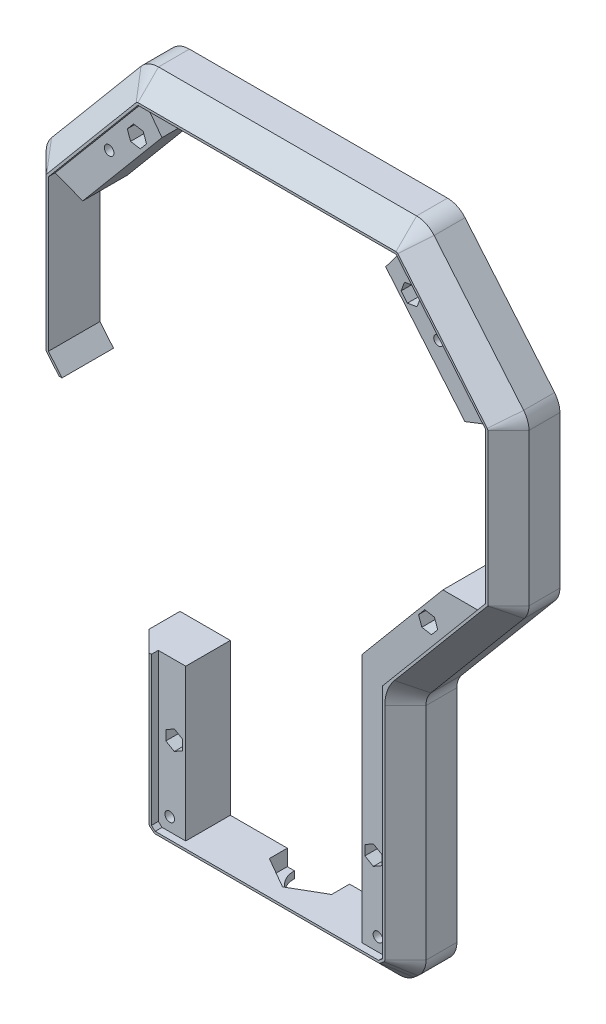
SolidWorks part; units mm, degrees
ref_plane "Plano frontal" through (0, 0, 0) normal (0, 0, 1) x (1, 0, 0)
ref_plane "Plano superior" through (0, 0, 0) normal (0, 1, 0) x (1, 0, 0)
ref_plane "Plano direito" through (0, 0, 0) normal (1, 0, 0) x (0, 0, -1)
sketch "Esboço1" plane through (0, 0, 0) normal (0, 0, 1) x (1, 0, 0)
  line L0 (-56.3875, 290.1973) -> (56.3875, 290.1973)
  line L1 (-60.5, 10.6056) -> (-60.5, 106.9588)
  line L2 (-62.6215, 112.7876) -> (-103.3785, 161.3599)
  line L3 (-105.5, 167.1887) -> (-105.5, 233.5849)
  line L4 (-48.8691, 270.1973) -> (48.8691, 270.1973)
  line L5 (0, 290.1973) -> (0, 0) construction
  line L6 (-64.0479, 286.6252) -> (-103.1604, 240.0128)
  line L7 (-83.5, 171.8956) -> (-83.5, 228.9258)
  line L8 (-83.5, 228.9258) -> (-48.8691, 270.1973)
  line L9 (-38.5, 19.1973) -> (38.5, 19.1973)
  line L10 (-38.5, 19.1973) -> (-38.5, 118.2666)
  line L11 (-38.5, 118.2666) -> (-83.5, 171.8956)
  line L12 (-56.9279, 2.9452) -> (-55.2496, 1.5369)
  line L13 (-48.8217, -0.8027) -> (48.8217, -0.8027)
  line L14 (56.9279, 2.9452) -> (55.2496, 1.5369)
  line L15 (38.5, 118.2666) -> (83.5, 171.8956)
  line L16 (38.5, 19.1973) -> (38.5, 118.2666)
  line L17 (83.5, 228.9258) -> (48.8691, 270.1973)
  line L18 (83.5, 171.8956) -> (83.5, 228.9258)
  line L19 (64.0479, 286.6252) -> (103.1604, 240.0128)
  line L20 (105.5, 167.1887) -> (105.5, 233.5849)
  line L21 (62.6215, 112.7876) -> (103.3785, 161.3599)
  line L22 (60.5, 10.6056) -> (60.5, 106.9588)
  arc A0 (-105.5, 233.5849) -> (-103.1604, 240.0128) centre (-95.5, 233.5849) cw
  arc A1 (-103.3785, 161.3599) -> (-105.5, 167.1887) centre (-96.4321, 167.1887) cw
  arc A2 (-60.5, 106.9588) -> (-62.6215, 112.7876) centre (-69.5679, 106.9588) ccw
  arc A3 (56.3875, 290.1973) -> (64.0479, 286.6252) centre (56.3875, 280.1973) cw
  arc A4 (-56.3875, 290.1973) -> (-64.0479, 286.6252) centre (-56.3875, 280.1973) ccw
  arc A5 (60.5, 106.9588) -> (62.6215, 112.7876) centre (69.5679, 106.9588) cw
  arc A6 (103.3785, 161.3599) -> (105.5, 167.1887) centre (96.4321, 167.1887) ccw
  arc A7 (105.5, 233.5849) -> (103.1604, 240.0128) centre (95.5, 233.5849) ccw
  arc A8 (56.9279, 2.9452) -> (60.5, 10.6056) centre (50.5, 10.6056) ccw
  arc A9 (55.2496, 1.5369) -> (48.8217, -0.8027) centre (48.8217, 9.1973) cw
  arc A10 (-48.8217, -0.8027) -> (-55.2496, 1.5369) centre (-48.8217, 9.1973) cw
  arc A11 (-60.5, 10.6056) -> (-56.9279, 2.9452) centre (-50.5, 10.6056) ccw
  point P27 (-105.5, 237.2246)
  point P33 (0, 19.1973)
  point P35 (0, -0.8027)
  point P40 (0, 270.1973)
  point P45 (0, 19.1973)
  point P46 (0, 19.1973)
  point P48 (0, 270.1973)
  point P50 (60.5, 5.9425)
  point P53 (0, 280)
  point P54 (52.4614, -0.8027)
  point P57 (-52.4614, -0.8027)
  point P60 (-60.5, 5.9425)
  dimension "D7" = 40
  dimension "D12" = 10
  dimension "D14" = 10
  dimension "D16" = 20
  dimension "D5" = 40
  dimension "D11" = 10
  dimension "D2" = 105.5
  dimension "D3" = 20
  dimension "D4" = 60.5
  dimension "D6" = 40
  dimension "D8" = 22
  dimension "D9" = 291
  dimension "D10" = 22
  dimension "D13" = 40
  dimension "D15" = 22
extrude "Ressalto-extrusão1" add sketch "Esboço1" along normal mid plane 45
chamfer "Chanfro1" distance 9 angle 45 24 edges at (0, -0.8027, 22.5) (-60.5, 58.7822, 22.5) (-61.0469, 110.0603, 22.5) (-83, 137.0738, 22.5) (0, 290.1973, 22.5) (-104.9531, 164.0873, 22.5) (-83.6042, 263.319, 22.5) (-105.5, 200.3868, 22.5) (61.0469, 110.0603, 22.5) (60.6137, 289.2604, 22.5) (-60.6137, 289.2604, 22.5) (-104.8969, 237.0051, 22.5) (-56.0887, 2.241, 22.5) (83.6042, 263.319, 22.5) (104.8969, 237.0051, 22.5) (105.5, 200.3868, 22.5) (104.9531, 164.0873, 22.5) (83, 137.0738, 22.5) (60.5, 58.7822, 22.5) (56.0887, 2.241, 22.5) (59.5631, 6.3794, 22.5) (52.2419, -0.1996, 22.5) (-52.2419, -0.1996, 22.5) (-59.5631, 6.3794, 22.5)
sketch "Esboço3" plane through (0, 0, 0) normal (0, 0, 1) x (1, 0, 0)
  line L1 (-722.7729, 507.4347) -> (416.458, 507.4347)
  line L2 (-722.7729, 507.4347) -> (-722.7729, -202.3634)
  line L3 (-722.7729, -202.3634) -> (416.458, -202.3634)
  line L4 (416.458, 507.4347) -> (416.458, -202.3634)
extrude "Corte-extrusão1" cut sketch "Esboço3" against normal up to next
sketch "Esboço4" plane through (0, 0, 22.5) normal (0, 0, 1) x (1, 0, 0)
  line L0 (38.5, 19.1973) -> (-38.5, 19.1973)
  line L1 (-38.5, 19.1973) -> (38.5, 19.1973) construction
  line L2 (56.3875, 281.1973) -> (-56.3875, 281.1973) construction
  line L3 (-38.5, 19.1973) -> (-38.5, 121.4891)
  line L5 (0, -6.7811) -> (0, 343.2781) construction
  line L6 (-38.5, 121.4891) -> (-83.5, 175.118)
  line L8 (-83.5, 175.118) -> (-83.5, 228.9258)
  line L9 (-83.5, 228.9258) -> (-48.8691, 270.1973)
  line L11 (-48.8691, 270.1973) -> (48.8691, 270.1973)
  line L12 (-48.8691, 270.1973) -> (48.8691, 270.1973) construction
  line L13 (56.3875, 280.1973) -> (-56.3875, 280.1973)
  line L14 (-56.3875, 280.1973) -> (-95.5, 233.5849)
  line L15 (-95.5, 233.5849) -> (-95.5, 167.5279)
  line L16 (-95.5, 167.5279) -> (-50.5, 113.899)
  line L18 (-50.5, 113.899) -> (-50.5, 10.6056)
  line L19 (-50.5, 10.6056) -> (-48.8217, 9.1973)
  line L20 (-48.8217, 9.1973) -> (48.8217, 9.1973)
  line L22 (-57.1535, 280.8401) -> (-96.266, 234.2277) construction
  line L24 (-96.5, 233.5849) -> (-96.5, 167.1887) construction
  line L25 (-51.5, 106.9588) -> (-51.5, 10.6056) construction
  line L26 (-48.8217, 8.1973) -> (48.8217, 8.1973) construction
  line L27 (-96.4841, 167.145) -> (-55.7271, 118.5727) construction
  line L32 (-51.1428, 9.8396) -> (-49.4645, 8.4313) construction
  line L33 (50.5, 10.6056) -> (48.8217, 9.1973)
  line L34 (50.5, 113.899) -> (50.5, 10.6056)
  line L35 (95.5, 167.5279) -> (50.5, 113.899)
  line L36 (95.5, 233.5849) -> (95.5, 167.5279)
  line L37 (56.3875, 280.1973) -> (95.5, 233.5849)
  line L38 (83.5, 228.9258) -> (48.8691, 270.1973)
  line L39 (83.5, 175.118) -> (83.5, 228.9258)
  line L40 (38.5, 121.4891) -> (83.5, 175.118)
  line L41 (38.5, 19.1973) -> (38.5, 121.4891)
  point P40 (0, 9.1973)
  point P44 (0, 280.1973)
  point P45 (0, 270.1973)
  point P46 (0, 19.1973)
  dimension "D1" = 1
  dimension "D2" = 1
  dimension "D3" = 1
  dimension "D4" = 1
  dimension "D5" = 1
  dimension "D6" = 1
  dimension "D7" = 1
extrude "Corte-extrusão5" cut sketch "Esboço4" against normal blind 3
sketch "Esboço5" plane through (0, 0, 19.5) normal (0, 0, 1) x (1, 0, 0)
  line L0 (-95.5, 233.5849) -> (-83.5, 228.9258)
  line L1 (-83.5, 228.9258) -> (-83.5, 171.8956)
  line L3 (-95.5, 167.5279) -> (-95.5, 233.5849)
  line L6 (0, -17.6729) -> (0, 329.9726) construction
  line L7 (-48.8691, 270.1973) -> (-56.3875, 280.1973)
  line L8 (-56.3875, 280.1973) -> (56.3875, 280.1973)
  line L9 (56.3875, 280.1973) -> (-56.3875, 280.1973) construction
  line L10 (-48.8691, 270.1973) -> (48.8691, 270.1973)
  line L11 (48.8691, 270.1973) -> (-48.8691, 270.1973) construction
  line L12 (-38.5, 19.1973) -> (-38.5, 9.1973)
  line L13 (-38.5, 19.1973) -> (38.5, 19.1973)
  line L14 (38.5, 19.1973) -> (-38.5, 19.1973) construction
  line L15 (-48.8217, 9.1973) -> (48.8217, 9.1973) construction
  line L16 (-38.5, 9.1973) -> (38.5, 9.1973)
  line L17 (-48.8217, 9.1973) -> (48.8217, 9.1973) construction
  line L18 (-95.5, 167.5279) -> (-83.5, 171.8956)
  line L19 (38.5, 9.1973) -> (38.5, 19.1973)
  line L20 (48.8691, 270.1973) -> (56.3875, 280.1973)
  line L21 (83.5, 171.8956) -> (95.5, 167.5279)
  line L23 (95.5, 167.5279) -> (95.5, 233.5849)
  line L25 (83.5, 228.9258) -> (83.5, 171.8956)
  line L26 (95.5, 233.5849) -> (83.5, 228.9258)
  point P38 (0, 9.1973)
  point P40 (0, 19.1973)
  point P41 (0, 270.1973)
  point P42 (0, 280.1973)
extrude "Corte-extrusão6" cut sketch "Esboço5" against normal up to next
sketch "Esboço7" plane through (0, 0, 22.5) normal (0, 0, 1) x (1, 0, 0)
  line L0 (-56.3875, 280.1973) -> (-95.5, 233.5849) construction
  line L1 (-50.5, 113.899) -> (-50.5, 10.6056) construction
  line L2 (-50.5, 113.899) -> (-50.5, 10.6056) construction
  line L3 (-95.5, 167.5279) -> (-50.5, 113.899) construction
  line L4 (56.3875, 280.1973) -> (-56.3875, 280.1973) construction
  line L5 (0, -30.1101) -> (0, 304.4524) construction
  circle A0 centre (-45.5, 14.9233) radius 2.1
  circle A1 centre (-43.5, 44.8566) radius 2.15
  circle A2 centre (-71.9753, 253.8419) radius 2.1
  circle A3 centre (-59.8361, 265.1973) radius 2.15
  circle A4 centre (59.8361, 265.1973) radius 2.15
  circle A5 centre (71.9753, 253.8419) radius 2.1
  circle A6 centre (43.5, 44.8566) radius 2.15
  circle A7 centre (45.5, 14.9233) radius 2.1
  circle A8 centre (-67.4311, 144.9668) radius 2.15
  circle A9 centre (67.4311, 144.9668) radius 2.15
  dimension "D1" = 5
  dimension "D2" = 7
  dimension "D3" = 7
  dimension "D4" = 5
  dimension "D5" = 7
  dimension "D6" = 30
  dimension "D8" = 15
  dimension "D7" = 26.3554
extrude "Corte-extrusão7" cut sketch "Esboço7" against normal through all
sketch "Esboço8" plane through (0, 0, 0) normal (0, 0, -1) x (-1, 0, 0)
  line L0 (0, -38.3704) -> (0, 336.2052) construction
  line L8 (-73.397, 257.7482) -> (-76.069, 254.5638)
  line L9 (-76.069, 254.5638) -> (-74.6473, 250.6576)
  line L10 (-74.6473, 250.6576) -> (-70.5535, 249.9357)
  line L11 (-70.5535, 249.9357) -> (-67.8815, 253.1201)
  line L12 (-67.8815, 253.1201) -> (-69.3033, 257.0263)
  line L19 (-45.5, 19.0803) -> (-49.1, 17.0018)
  line L20 (-49.1, 17.0018) -> (-49.1, 12.8449)
  line L21 (-49.1, 12.8449) -> (-45.5, 10.7664)
  line L22 (-45.5, 10.7664) -> (-41.9, 12.8449)
  line L23 (-41.9, 12.8449) -> (-41.9, 17.0018)
  line L24 (-41.9, 17.0018) -> (-45.5, 19.0803)
  line L25 (41.9, 17.0018) -> (45.5, 19.0803)
  line L26 (41.9, 12.8449) -> (41.9, 17.0018)
  line L27 (45.5, 10.7664) -> (41.9, 12.8449)
  line L28 (49.1, 12.8449) -> (45.5, 10.7664)
  line L29 (49.1, 17.0018) -> (49.1, 12.8449)
  line L30 (45.5, 19.0803) -> (49.1, 17.0018)
  line L37 (-69.3033, 257.0263) -> (-73.397, 257.7482)
  line L38 (76.069, 254.5638) -> (73.397, 257.7482)
  line L39 (73.397, 257.7482) -> (69.3033, 257.0263)
  line L40 (69.3033, 257.0263) -> (67.8815, 253.1201)
  line L41 (67.8815, 253.1201) -> (70.5535, 249.9357)
  line L42 (70.5535, 249.9357) -> (74.6473, 250.6576)
  line L43 (74.6473, 250.6576) -> (76.069, 254.5638)
  line L56 (67.5809, 147.4789) -> (71.561, 146.7771)
  line L57 (64.9831, 144.383) -> (67.5809, 147.4789)
  line L58 (66.3654, 140.5853) -> (64.9831, 144.383)
  line L59 (70.3454, 139.8835) -> (66.3654, 140.5853)
  line L60 (72.9432, 142.9794) -> (70.3454, 139.8835)
  line L61 (71.561, 146.7771) -> (72.9432, 142.9794)
  line L62 (48.8691, 270.1973) -> (83.5, 228.9258) construction
  line L63 (-48.8691, 270.1973) -> (-83.5, 228.9258) construction
  circle A1 centre (-71.9753, 253.8419) radius 3.6 construction
  circle A3 centre (-45.5, 14.9233) radius 3.6 construction
  circle A4 centre (45.5, 14.9233) radius 3.6 construction
  circle A6 centre (71.9753, 253.8419) radius 3.6 construction
  circle A9 centre (68.9632, 143.6812) radius 3.5 construction
  point P0 (0, 0)
extrude "Corte-extrusão8" cut sketch "Esboço8" against normal blind 10
sketch "Esboço9" plane through (0, 0, 22.5) normal (0, 0, 1) x (1, 0, 0)
  line L0 (-116.4566, 160.4281) -> (-23.6678, 160.4281)
  line L1 (-23.6678, 160.4281) -> (-23.6678, 75.3657)
  line L2 (-23.6678, 75.3657) -> (-116.4566, 75.3657)
  line L3 (-116.4566, 75.3657) -> (-116.4566, 160.4281)
extrude "Corte-extrusão9" cut sketch "Esboço9" against normal through all
sketch "Esboço10" plane through (0, 0, 19.5) normal (0, 0, 1) x (1, 0, 0)
  line L0 (-95.5, 167.5279) -> (-83.5, 171.8956)
  line L1 (-83.5, 171.8956) -> (-73.8777, 160.4281)
  line L2 (-73.8777, 160.4281) -> (-89.5426, 160.4281)
  line L3 (-89.5426, 160.4281) -> (-95.5, 167.5279)
  line L4 (0, 297.577) -> (0, -32.5726) construction
  line L5 (89.5426, 160.4281) -> (95.5, 167.5279)
  line L6 (73.8777, 160.4281) -> (89.5426, 160.4281)
  line L7 (83.5, 171.8956) -> (73.8777, 160.4281)
  line L8 (95.5, 167.5279) -> (83.5, 171.8956)
extrude "Corte-extrusão10" cut sketch "Esboço10" against normal up to next
sketch "Esboço11" plane through (0, 9.1973, 0) normal (0, 1, 0) x (1, 0, 0)
  line L1 (0, -15.7039) -> (13.6, -7.852)
  line L2 (13.6, -7.852) -> (13.6, 7.852)
  line L3 (13.6, 7.852) -> (0, 15.7039)
  line L4 (0, 15.7039) -> (-13.6, 7.852)
  line L5 (-13.6, 7.852) -> (-13.6, -7.852)
  line L6 (-13.6, -7.852) -> (0, -15.7039)
  circle A0 centre (0, 0) radius 13.6 construction
extrude "Corte-extrusão11" cut sketch "Esboço11" against normal blind 7
sketch "Esboço12" plane through (0, -0.8027, 0) normal (0, -1, 0) x (1, 0, 0)
  circle A0 centre (0, 0) radius 10.5
extrude "Corte-extrusão12" cut sketch "Esboço12" against normal blind 7
sketch "Esboço13" plane through (0, 0, 19.5) normal (0, 0, 1) x (1, 0, 0)
  line L0 (-48.8691, 270.1973) -> (-83.5, 228.9258) construction
  line L1 (-57.0899, 268.4702) -> (-61.2974, 269.2121)
  line L2 (-61.2974, 269.2121) -> (-64.0436, 265.9392)
  line L3 (-64.0436, 265.9392) -> (-62.5824, 261.9245)
  line L4 (-62.5824, 261.9245) -> (-58.3749, 261.1826)
  line L5 (-58.3749, 261.1826) -> (-55.6287, 264.4555)
  line L6 (-55.6287, 264.4555) -> (-57.0899, 268.4702)
  line L7 (83.5, 228.9258) -> (48.8691, 270.1973) construction
  line L8 (61.2974, 269.2121) -> (57.0899, 268.4702)
  line L9 (57.0899, 268.4702) -> (55.6287, 264.4555)
  line L10 (55.6287, 264.4555) -> (58.3749, 261.1826)
  line L11 (58.3749, 261.1826) -> (62.5824, 261.9245)
  line L12 (62.5824, 261.9245) -> (64.0436, 265.9392)
  line L13 (64.0436, 265.9392) -> (61.2974, 269.2121)
  line L14 (-38.5, 75.3657) -> (-38.5, 9.1973) construction
  line L15 (-47.2, 46.9928) -> (-47.2, 42.7204)
  line L16 (-47.2, 42.7204) -> (-43.5, 40.5842)
  line L17 (-43.5, 40.5842) -> (-39.8, 42.7204)
  line L18 (-39.8, 42.7204) -> (-39.8, 46.9928)
  line L19 (-39.8, 46.9928) -> (-43.5, 49.129)
  line L20 (-43.5, 49.129) -> (-47.2, 46.9928)
  line L21 (38.5, 9.1973) -> (38.5, 118.2666) construction
  line L22 (47.2, 46.9928) -> (43.5, 49.129)
  line L23 (43.5, 49.129) -> (39.8, 46.9928)
  line L24 (39.8, 46.9928) -> (39.8, 42.7204)
  line L25 (39.8, 42.7204) -> (43.5, 40.5842)
  line L26 (43.5, 40.5842) -> (47.2, 42.7204)
  line L27 (47.2, 42.7204) -> (47.2, 46.9928)
  line L28 (38.5, 118.2666) -> (73.8777, 160.4281) construction
  line L29 (70.1773, 148.2396) -> (65.9699, 148.9815)
  line L30 (65.9699, 148.9815) -> (63.2236, 145.7087)
  line L31 (63.2236, 145.7087) -> (64.6849, 141.6939)
  line L32 (64.6849, 141.6939) -> (68.8923, 140.952)
  line L33 (68.8923, 140.952) -> (71.6386, 144.2249)
  line L34 (71.6386, 144.2249) -> (70.1773, 148.2396)
  circle A0 centre (-59.8361, 265.1973) radius 3.7 construction
  circle A1 centre (59.8361, 265.1973) radius 3.7 construction
  circle A2 centre (-43.5, 44.8566) radius 3.7 construction
  circle A3 centre (43.5, 44.8566) radius 3.7 construction
  circle A4 centre (67.4311, 144.9668) radius 3.7 construction
extrude "Corte-extrusão13" cut sketch "Esboço13" against normal blind 10
